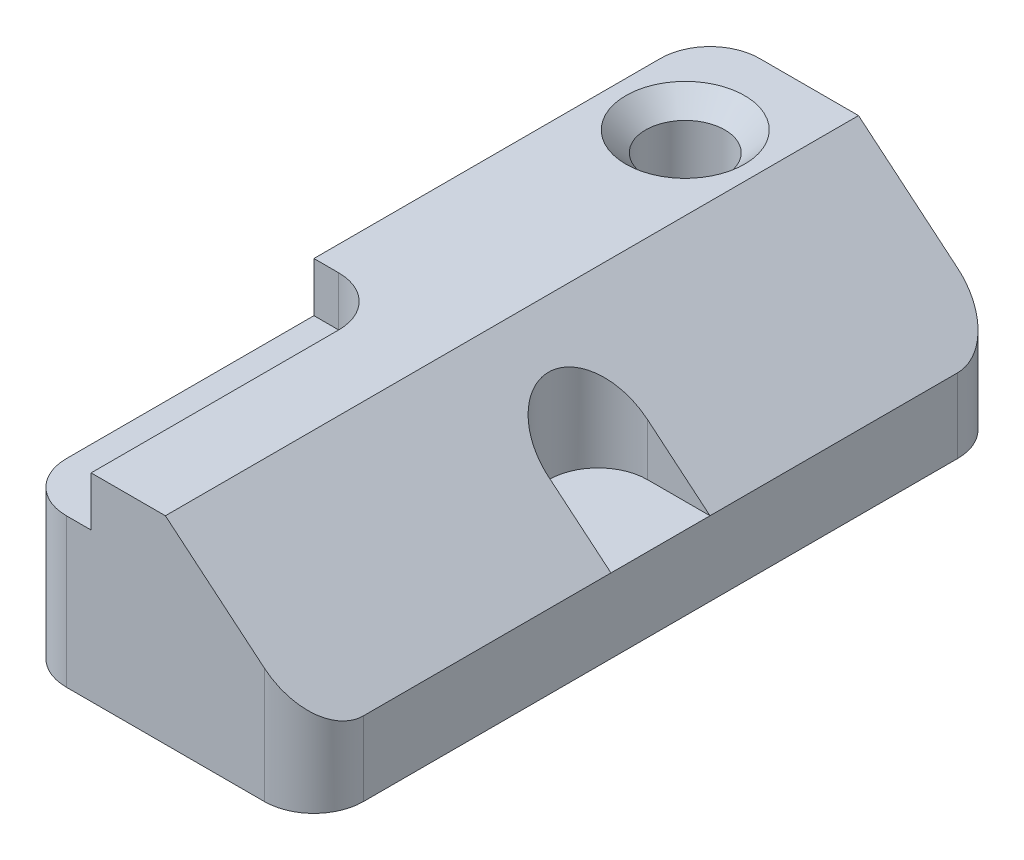
SolidWorks part; units mm, degrees
material "Plain Carbon Steel"
ref_plane "Front Plane" through (0, 0, 0) normal (0, 0, 1) x (1, 0, 0)
ref_plane "Top Plane" through (0, 0, 0) normal (0, 1, 0) x (1, 0, 0)
ref_plane "Right Plane" through (0, 0, 0) normal (1, 0, 0) x (0, 0, -1)
sketch "Sketch1" plane through (0, 0, 0) normal (0, 0, 1) x (1, 0, 0)
  line L0 (0, 0) -> (0, 50.8)
  line L1 (0, 50.8) -> (38.1, 50.8)
  line L2 (38.1, 50.8) -> (76.2, 19.05)
  line L3 (76.2, 19.05) -> (76.2, 0)
  line L4 (76.2, 0) -> (0, 0)
  dimension "D1" = 50.8
  dimension "D2" = 38.1
  dimension "D3" = 76.2
  dimension "D4" = 19.05
extrude "Boss-Extrude1" add sketch "Sketch1" against normal blind 177.8
sketch "Sketch8" plane through (0, 50.8, 0) normal (0, 1, 0) x (1, 0, 0)
  line L0 (38.1, 177.8) -> (0, 177.8) construction
  line L1 (0, 177.8) -> (0, 0) construction
  circle A0 centre (19.05, 152.4) radius 10.16
  dimension "D1" = 20.32
  dimension "D2" = 25.4
  dimension "D3" = 19.05
extrude "Cut-Extrude1" cut sketch "Sketch8" against normal through all
chamfer "Chamfer1" distance 5.08 angle 45 1 edges at (19.05, 50.8, -142.24)
sketch "Sketch9" plane through (0, 50.8, 0) normal (0, 1, 0) x (1, 0, 0)
  line L1 (0, 0) -> (19.05, 0)
  line L2 (0, 0) -> (0, 76.2)
  line L3 (0, 76.2) -> (19.05, 76.2)
  line L4 (19.05, 0) -> (19.05, 76.2)
  dimension "D1" = 76.2
  dimension "D2" = 19.05
extrude "Cut-Extrude2" cut sketch "Sketch9" against normal blind 12.7 contours L2 L1 L4 L3
fillet "Fillet1" radius 12.7 1 edges at (19.05, 44.45, -76.2)
sketch "Sketch10" plane through (0, 50.8, 0) normal (0, 1, 0) x (1, 0, 0)
  line L0 (76.2, 101.6) -> (60.198, 101.6)
  line L1 (76.2, 177.8) -> (76.2, 0) construction
  line L2 (60.198, 76.2) -> (76.2, 76.2)
  line L3 (76.2, 76.2) -> (76.2, 101.6)
  line L4 (76.2, 88.9) -> (0, 88.9) construction
  line L5 (0, 0) -> (0, 76.2) construction
  arc A0 (60.198, 101.6) -> (60.198, 76.2) centre (60.198, 88.9) ccw
  point P11 (60.198, 63.5)
  dimension "D2" = 12.7
  dimension "D1" = 16.002
extrude "Cut-Extrude3" cut sketch "Sketch10" against normal up to vertex (31.75 mm away)
fillet "Fillet2" radius 12.7 4 edges at (76.2, 9.525, -177.8) (0, 25.4, -177.8) (0, 19.05, 0) (76.2, 9.525, 0)
